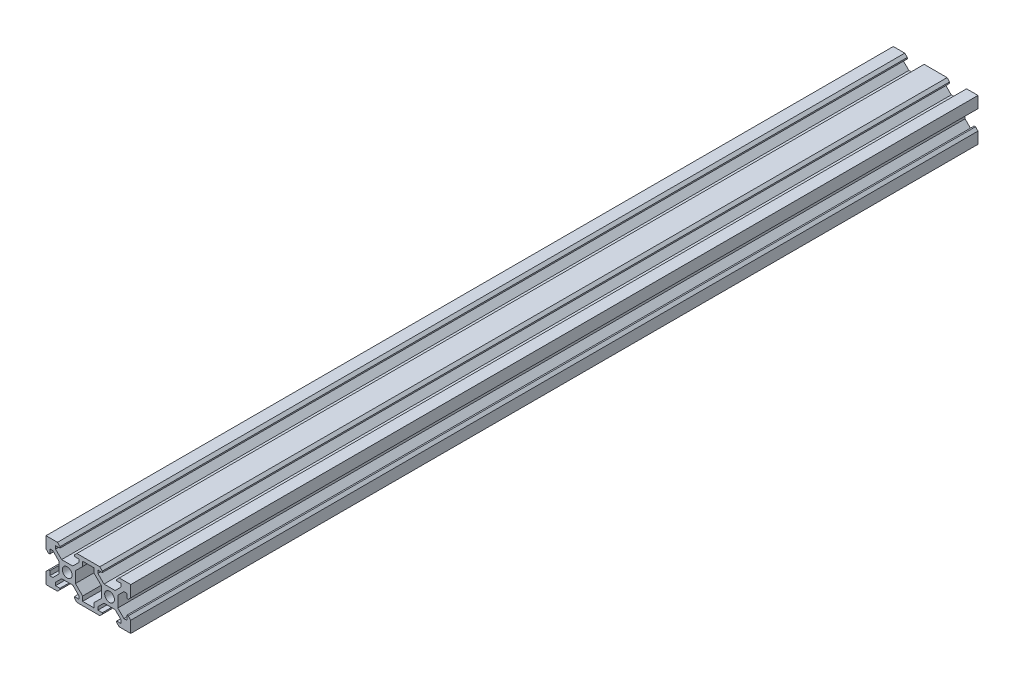
SolidWorks part; units mm, degrees
ref_plane "Front Plane" through (0, 0, 0) normal (0, 0, 1) x (1, 0, 0)
ref_plane "Top Plane" through (0, 0, 0) normal (0, 1, 0) x (1, 0, 0)
ref_plane "Right Plane" through (0, 0, 0) normal (1, 0, 0) x (0, 0, -1)
sketch "Sketch1" plane through (0, 0, 0) normal (0, 0, 1) x (1, 0, 0)
  line L1 (0, 0) -> (40, 0)
  line L2 (0, 0) -> (0, 20)
  line L3 (0, 20) -> (40, 20)
  line L4 (40, 0) -> (40, 20)
  dimension "D1" = 40
  dimension "D2" = 20
extrude "Boss-Extrude1" add sketch "Sketch1" against normal blind 400
sketch "Sketch2" plane through (0, 0, 0) normal (0, 0, 1) x (1, 0, 0)
  line L0 (14.58, 20) -> (13.395, 18.815)
  line L1 (20, 20) -> (20, 0) construction
  line L2 (40, 20) -> (0, 20) construction
  line L15 (0, 0) -> (40, 0) construction
  line L16 (0, 20) -> (20, 0) construction
  line L29 (0, 10) -> (20, 10) construction
  line L30 (13.395, 18.815) -> (13.395, 18.2)
  line L79 (13.395, 18.2) -> (15.5, 18.2)
  line L80 (15.5, 18.2) -> (15.5, 16.7728)
  line L81 (15.5, 16.7728) -> (12.6272, 13.9)
  line L84 (12.6272, 13.9) -> (7.3728, 13.9)
  line L85 (7.3728, 13.9) -> (4.5, 16.7728)
  line L86 (4.5, 16.7728) -> (4.5, 18.2)
  line L87 (4.5, 18.2) -> (6.605, 18.2)
  line L88 (6.605, 18.2) -> (6.605, 18.815)
  line L89 (6.605, 18.815) -> (5.42, 20)
  line L90 (5.42, 20) -> (14.58, 20)
  line L91 (0, 20) -> (0, 0) construction
  line L92 (1.185, 13.395) -> (0, 14.58)
  line L93 (1.8, 13.395) -> (1.185, 13.395)
  line L94 (1.8, 15.5) -> (1.8, 13.395)
  line L95 (3.2272, 15.5) -> (1.8, 15.5)
  line L96 (6.1, 12.6272) -> (3.2272, 15.5)
  line L97 (6.1, 7.3728) -> (6.1, 12.6272)
  line L98 (3.2272, 4.5) -> (6.1, 7.3728)
  line L99 (1.8, 4.5) -> (3.2272, 4.5)
  line L100 (1.8, 6.605) -> (1.8, 4.5)
  line L101 (1.185, 6.605) -> (1.8, 6.605)
  line L102 (0, 5.42) -> (1.185, 6.605)
  line L103 (0, 14.58) -> (0, 5.42)
  line L104 (38.2, 13.395) -> (38.815, 13.395)
  line L105 (38.2, 15.5) -> (38.2, 13.395)
  line L106 (36.7728, 15.5) -> (38.2, 15.5)
  line L107 (33.9, 12.6272) -> (36.7728, 15.5)
  line L108 (33.9, 7.3728) -> (33.9, 12.6272)
  line L109 (36.7728, 4.5) -> (33.9, 7.3728)
  line L110 (38.2, 4.5) -> (36.7728, 4.5)
  line L111 (38.2, 6.605) -> (38.2, 4.5)
  line L112 (38.815, 6.605) -> (38.2, 6.605)
  line L113 (40, 5.42) -> (38.815, 6.605)
  line L114 (40, 14.58) -> (40, 5.42)
  line L115 (38.815, 13.395) -> (40, 14.58)
  line L116 (33.395, 18.815) -> (34.58, 20)
  line L117 (33.395, 18.2) -> (33.395, 18.815)
  line L118 (35.5, 18.2) -> (33.395, 18.2)
  line L119 (35.5, 16.7728) -> (35.5, 18.2)
  line L120 (32.6272, 13.9) -> (35.5, 16.7728)
  line L121 (27.3728, 13.9) -> (32.6272, 13.9)
  line L122 (24.5, 16.7728) -> (27.3728, 13.9)
  line L123 (24.5, 18.2) -> (24.5, 16.7728)
  line L124 (26.605, 18.2) -> (24.5, 18.2)
  line L125 (26.605, 18.815) -> (26.605, 18.2)
  line L126 (25.42, 20) -> (26.605, 18.815)
  line L127 (34.58, 20) -> (25.42, 20)
  line L128 (33.395, 1.8) -> (33.395, 1.185)
  line L129 (35.5, 1.8) -> (33.395, 1.8)
  line L130 (35.5, 3.2272) -> (35.5, 1.8)
  line L131 (32.6272, 6.1) -> (35.5, 3.2272)
  line L132 (27.3728, 6.1) -> (32.6272, 6.1)
  line L133 (24.5, 3.2272) -> (27.3728, 6.1)
  line L134 (24.5, 1.8) -> (24.5, 3.2272)
  line L135 (26.605, 1.8) -> (24.5, 1.8)
  line L136 (26.605, 1.185) -> (26.605, 1.8)
  line L137 (25.42, 0) -> (26.605, 1.185)
  line L138 (34.58, 0) -> (25.42, 0)
  line L139 (33.395, 1.185) -> (34.58, 0)
  line L140 (6.605, 1.185) -> (5.42, 0)
  line L141 (6.605, 1.8) -> (6.605, 1.185)
  line L142 (4.5, 1.8) -> (6.605, 1.8)
  line L143 (4.5, 3.2272) -> (4.5, 1.8)
  line L144 (7.3728, 6.1) -> (4.5, 3.2272)
  line L145 (12.6272, 6.1) -> (7.3728, 6.1)
  line L146 (15.5, 3.2272) -> (12.6272, 6.1)
  line L147 (15.5, 1.8) -> (15.5, 3.2272)
  line L148 (13.395, 1.8) -> (15.5, 1.8)
  line L149 (13.395, 1.185) -> (13.395, 1.8)
  line L150 (14.58, 0) -> (13.395, 1.185)
  line L151 (5.42, 0) -> (14.58, 0)
  point P23 (10, 20)
  point P24 (10, 10)
  point P26 (10, 13.9)
  dimension "D1" = 90
  dimension "D2" = 9.16
  dimension "D3" = 6.79
  dimension "D4" = 11
  dimension "D5" = 1.8
  dimension "D6" = 4.3
  dimension "D7" = 0.9
extrude "Cut-Extrude3" cut sketch "Sketch2" against normal through all
sketch "Sketch5" plane through (0, 0, 0) normal (0, 0, 1) x (1, 0, 0)
  line L0 (17.3, 1.8) -> (22.7, 1.8)
  line L5 (17.3, 16.0272) -> (17.3, 18.2)
  line L6 (13.9, 12.6272) -> (17.3, 16.0272)
  line L7 (17.3, 16.0272) -> (17.3, 18.2)
  line L8 (13.9, 12.6272) -> (17.3, 16.0272)
  line L17 (22.7, 16.0272) -> (26.1, 12.6272)
  line L18 (22.7, 18.2) -> (22.7, 16.0272)
  line L19 (22.7, 16.0272) -> (26.1, 12.6272)
  line L20 (22.7, 18.2) -> (22.7, 16.0272)
  line L24 (22.7, 3.9728) -> (22.7, 1.8)
  line L25 (26.1, 7.3728) -> (22.7, 3.9728)
  line L26 (22.7, 3.9728) -> (22.7, 1.8)
  line L27 (26.1, 7.3728) -> (22.7, 3.9728)
  line L29 (13.9, 12.6272) -> (13.9, 7.3728)
  line L30 (26.1, 12.6272) -> (26.1, 7.3728)
  line L31 (17.3, 1.8) -> (17.3, 3.9728)
  line L32 (17.3, 3.9728) -> (13.9, 7.3728)
  line L33 (17.3, 1.8) -> (17.3, 3.9728)
  line L34 (17.3, 3.9728) -> (13.9, 7.3728)
  line L35 (17.3, 18.2) -> (22.7, 18.2)
  dimension "D1" = 1.8
  dimension "D2" = 1.8
  dimension "D3" = 1.8
  dimension "D4" = 1.8
extrude "Cut-Extrude4" cut sketch "Sketch5" against normal through all
sketch "Sketch6" plane through (0, 0, 0) normal (0, 0, 1) x (1, 0, 0)
  line L0 (6.1, 10) -> (13.9, 10) construction
  line L1 (6.1, 7.3728) -> (6.1, 12.6272) construction
  line L2 (13.9, 12.6272) -> (13.9, 7.3728) construction
  line L3 (10, 13.9) -> (10, 6.1) construction
  line L4 (7.3728, 13.9) -> (12.6272, 13.9) construction
  line L5 (12.6272, 6.1) -> (7.3728, 6.1) construction
  line L6 (20, 20) -> (20, 0) construction
  line L7 (25.42, 20) -> (14.58, 20) construction
  line L8 (14.58, 0) -> (25.42, 0) construction
  circle A0 centre (10, 10) radius 2.3
  circle A1 centre (30, 10) radius 2.3
  dimension "D1" = 4.6
extrude "Cut-Extrude5" cut sketch "Sketch6" against normal through all
